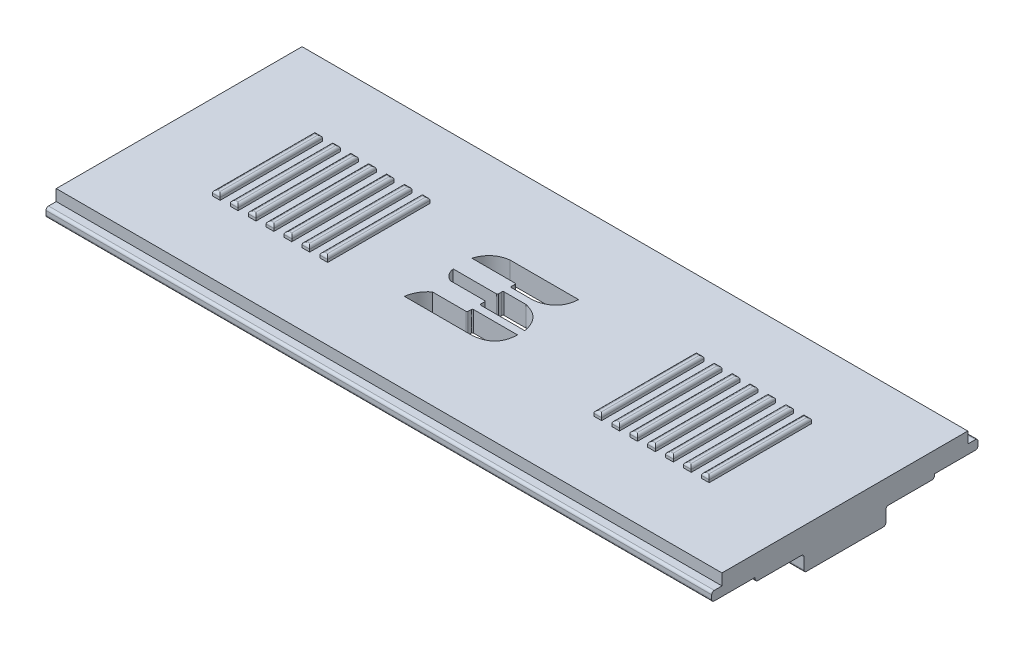
SolidWorks part; units mm, degrees
ref_plane "Front Plane" through (0, 0, 0) normal (0, 0, 1) x (1, 0, 0)
ref_plane "Top Plane" through (0, 0, 0) normal (0, 1, 0) x (1, 0, 0)
ref_plane "Right Plane" through (0, 0, 0) normal (1, 0, 0) x (0, 0, -1)
sketch "Sketch1" plane through (0, 0, 0) normal (0, 1, 0) x (1, 0, 0)
  line L1 (0, 0) -> (-65, 0)
  line L2 (0, 0) -> (0, 28)
  line L3 (0, 28) -> (-65, 28)
  line L4 (-65, 0) -> (-65, 28)
  dimension "D1" = 65
  dimension "D2" = 28
extrude "Boss-Extrude1" add sketch "Sketch1" along normal blind 2
sketch "Sketch2" plane through (0, 2, 0) normal (0, 1, 0) x (1, 0, 0)
  line L0 (-65, 28) -> (-65, 0) construction
  line L2 (-39, 9.4351) -> (-39, 19.8)
  line L3 (-39, 19.8) -> (-45.078, 19.8)
  line L5 (0, 28) -> (-65, 28) construction
  line L6 (-45.078, 19.8) -> (-45.078, 13.1703)
  line L7 (-45.078, 13.1703) -> (-39, 13.1703)
  line L8 (-39, 9.4351) -> (-45.078, 9.4351)
  line L9 (-45.078, 9.4351) -> (-45.078, 16.0649)
  line L10 (-45.078, 16.0649) -> (-39, 16.0649)
  line L11 (-45.078, 16.0649) -> (-45.078, 13.1703)
  point P6 (-42.039, 19.8)
  dimension "D1" = 26
  dimension "D2" = 8.2
sketch "Sketch5" plane through (0, 2, 0) normal (0, 1, 0) x (1, 0, 0)
  line L69 (-34.5, 28) -> (-34.5, 0) construction
  line L70 (-30.1108, 18.1128) -> (-36.82, 18.1128)
  line L86 (-34.5, 14) -> (-65, 14) construction
  line L87 (-65, 28) -> (-65, 0) construction
  line L157 (-38.8269, 16.4025) -> (-34.6166, 16.4025)
  line L158 (-34.5132, 16.3274) -> (-34.5132, 15.9551)
  line L159 (-34.4285, 15.8453) -> (-32.2293, 15.8453)
  line L160 (-34.4186, 15.1333) -> (-32.2791, 15.1333)
  line L161 (-34.5132, 14.6729) -> (-34.5132, 15.0121)
  line L162 (-34.6166, 14.5874) -> (-38.8269, 14.5874)
  line L163 (-37.9572, 13.4446) -> (-34.6166, 13.4446)
  line L164 (-34.5132, 13.3644) -> (-34.5132, 12.9776)
  line L165 (-34.4131, 12.859) -> (-30.1108, 12.859)
  line L166 (-30.1108, 12.1455) -> (-34.4131, 12.1455)
  line L167 (-34.5132, 12.0357) -> (-34.5132, 11.725)
  line L168 (-34.6166, 11.627) -> (-37.9062, 11.627)
  line L169 (-38.8924, 9.8833) -> (-32.2102, 9.8833)
  spline S0 degree 2 poles (-30.1108, 18.1128) (-30.2266, 16.1766) (-32.2293, 15.8453) knots 0 0 0 1 1 1
  spline S1 degree 2 poles (-36.82, 18.1128) (-38.3422, 17.8962) (-38.8269, 16.4025) knots 0 0 0 1 1 1
  spline S2 degree 2 poles (-32.2791, 15.1333) (-30.444, 14.7354) (-30.1108, 12.859) knots 0 0 0 1 1 1
  spline S3 degree 2 poles (-38.8269, 14.5874) (-38.7018, 13.7846) (-37.9572, 13.4446) knots 0 0 0 1 1 1
  spline S4 degree 2 poles (-37.9062, 11.627) (-38.7379, 10.948) (-38.8924, 9.8833) knots 0 0 0 1 1 1
  spline S5 degree 2 poles (-30.1108, 12.1455) (-30.1355, 10.1172) (-32.2102, 9.8833) knots 0 0 0 1 1 1
  spline S6 degree 2 poles (-34.6166, 16.4025) (-34.5203, 16.4078) (-34.5132, 16.3274) knots 0 0 0 1 1 1
  spline S7 degree 2 poles (-34.5132, 15.9551) (-34.5132, 15.8685) (-34.4285, 15.8453) knots 0 0 0 1 1 1
  spline S8 degree 2 poles (-34.4186, 15.1333) (-34.5097, 15.1098) (-34.5132, 15.0121) knots 0 0 0 1 1 1
  spline S9 degree 2 poles (-34.5132, 14.6729) (-34.528, 14.5885) (-34.6166, 14.5874) knots 0 0 0 1 1 1
  spline S10 degree 2 poles (-34.6166, 13.4446) (-34.5199, 13.4532) (-34.5132, 13.3644) knots 0 0 0 1 1 1
  spline S11 degree 2 poles (-34.5132, 12.9776) (-34.5006, 12.8836) (-34.4131, 12.859) knots 0 0 0 1 1 1
  spline S12 degree 2 poles (-34.4131, 12.1455) (-34.5019, 12.1303) (-34.5132, 12.0357) knots 0 0 0 1 1 1
  spline S13 degree 2 poles (-34.6166, 11.627) (-34.5056, 11.6151) (-34.5132, 11.725) knots 0 0 0 1 1 1
  dimension "D1" = 30.5
extrude "Cut-Extrude4" cut sketch "Sketch5" against normal blind 10
fillet "Fillet1" radius 1 4 edges at (0, 1, -28) (0, 1, 0) (-65, 1, 0) (-65, 1, -28)
sketch "Sketch7" plane through (0, 0, 0) normal (1, 0, 0) x (0, 0, -1)
  line L0 (26, 2) -> (26, 0.9)
  line L1 (26, 0.9) -> (27, 0.9)
  line L2 (27, 0.9) -> (27, 0)
  line L3 (27, 0) -> (1, 0)
  line L4 (1, 0) -> (1, 0.9)
  line L5 (1, 0.9) -> (2, 0.9)
  line L6 (2, 0.9) -> (2, 2)
  line L7 (26, 2) -> (2, 2)
  line L8 (1, 0) -> (27, 0) construction
  line L11 (1, 2) -> (1, 0) construction
  dimension "D1" = 0.9
  dimension "D2" = 1.1
  dimension "D3" = 24
  dimension "D4" = 1
extrude "Cut-Extrude6" cut sketch "Sketch7" against normal through all flip side to cut
sketch "Sketch9" plane through (0, 2, 0) normal (0, 1, 0) x (1, 0, 0)
  line L1 (-55, 19) -> (-54.25, 19)
  line L2 (-55, 19) -> (-55, 9)
  line L3 (-55, 9) -> (-54.25, 9)
  line L4 (-54.25, 19) -> (-54.25, 9)
  line L5 (-53.25, 9) -> (-52.5, 9)
  line L6 (-53.25, 9) -> (-53.25, 19)
  line L7 (-53.25, 19) -> (-52.5, 19)
  line L8 (-52.5, 9) -> (-52.5, 19)
  line L9 (-51.5, 9) -> (-50.75, 9)
  line L10 (-51.5, 9) -> (-51.5, 19)
  line L11 (-51.5, 19) -> (-50.75, 19)
  line L12 (-50.75, 9) -> (-50.75, 19)
  line L13 (-49.75, 9) -> (-49, 9)
  line L14 (-49.75, 9) -> (-49.75, 19)
  line L15 (-49.75, 19) -> (-49, 19)
  line L16 (-49, 9) -> (-49, 19)
  line L32 (-65, 26) -> (-65, 2) construction
  line L33 (-65, 26) -> (0, 26) construction
  line L34 (-32.5, 26) -> (-32.5, 20.1111) construction
  line L35 (-48, 19) -> (-47.25, 19)
  line L36 (-48, 19) -> (-48, 9)
  line L37 (-48, 9) -> (-47.25, 9)
  line L38 (-47.25, 19) -> (-47.25, 9)
  line L39 (-19.5, 19) -> (-19.5, 9)
  line L60 (-56, 19) -> (-56.75, 19)
  line L61 (-56, 19) -> (-56, 9)
  line L62 (-56, 9) -> (-56.75, 9)
  line L63 (-56.75, 19) -> (-56.75, 9)
  line L64 (-46.25, 19) -> (-45.5, 19)
  line L65 (-46.25, 19) -> (-46.25, 9)
  line L66 (-46.25, 9) -> (-45.5, 9)
  line L67 (-45.5, 19) -> (-45.5, 9)
  line L68 (-18.75, 9) -> (-19.5, 9)
  line L69 (-18.75, 19) -> (-18.75, 9)
  line L70 (-18.75, 19) -> (-19.5, 19)
  line L71 (-8.25, 19) -> (-8.25, 9)
  line L72 (-9, 9) -> (-8.25, 9)
  line L73 (-9, 19) -> (-9, 9)
  line L74 (-9, 19) -> (-8.25, 19)
  line L75 (-17.75, 19) -> (-17.75, 9)
  line L76 (-17, 9) -> (-17.75, 9)
  line L77 (-17, 19) -> (-17, 9)
  line L78 (-17, 19) -> (-17.75, 19)
  line L79 (-16, 9) -> (-16, 19)
  line L80 (-15.25, 19) -> (-16, 19)
  line L81 (-15.25, 9) -> (-15.25, 19)
  line L82 (-15.25, 9) -> (-16, 9)
  line L83 (-14.25, 9) -> (-14.25, 19)
  line L84 (-13.5, 19) -> (-14.25, 19)
  line L85 (-13.5, 9) -> (-13.5, 19)
  line L86 (-13.5, 9) -> (-14.25, 9)
  line L87 (-12.5, 9) -> (-12.5, 19)
  line L88 (-11.75, 19) -> (-12.5, 19)
  line L89 (-11.75, 9) -> (-11.75, 19)
  line L90 (-11.75, 9) -> (-12.5, 9)
  line L91 (-10.75, 19) -> (-10.75, 9)
  line L92 (-10, 9) -> (-10.75, 9)
  line L93 (-10, 19) -> (-10, 9)
  line L94 (-10, 19) -> (-10.75, 19)
  point P25 (-32.5, 26)
  dimension "D1" = 0.75
  dimension "D2" = 10
  dimension "D3" = 1
  dimension "D4" = 1
  dimension "D5" = 1
  dimension "D6" = 10
  dimension "D7" = 7
  dimension "D8" = 1
  dimension "D9" = 1
  dimension "D10" = 1
sketch "Sketch10" plane through (0, 0, 0) normal (0, -1, 0) x (1, 0, 0)
  line L0 (0, -1) -> (0, -27) construction
  line L1 (0, -18) -> (-4, -18)
  line L2 (0, -18) -> (0, -10)
  line L3 (0, -10) -> (-4, -10)
  line L4 (-4, -18) -> (-4, -10)
  line L5 (-65, -27) -> (0, -27) construction
  line L6 (-65, -1) -> (0, -1) construction
  point P8 (-2, -10)
  dimension "D1" = 9
  dimension "D2" = 9
  dimension "D3" = 4
extrude "Boss-Extrude2" add sketch "Sketch10" along normal blind 2
fillet "Fillet2" radius 0.25 6 edges at (-2, 0, -18) (-2, -2, -18) (-4, 0, -14) (-4, -2, -14) (-2, 0, -10) (-2, -2, -10)
fillet "Fillet3" radius 0.25 4 edges at (-32.5, 0.9, -1) (-32.5, 0, -1) (-32.5, 0.9, -27) (-32.5, 0, -27)
sketch "Sketch11" plane through (0, 0, 0) normal (0, -1, 0) x (1, 0, 0)
  line L0 (0, -18.25) -> (0, -26.75) construction
  line L1 (0, -22.75) -> (-3.5, -22.75)
  line L2 (0, -22.75) -> (0, -5.25)
  line L3 (0, -5.25) -> (-3.5, -5.25)
  line L4 (-3.5, -22.75) -> (-3.5, -5.25)
  line L5 (0, -17.75) -> (0, -10.25) construction
  line L6 (0, -10.25) -> (-3.75, -10.25) construction
  point P8 (0, -14)
  point P9 (0, -14)
  dimension "D1" = 3.5
  dimension "D2" = 0
  dimension "D3" = 5
extrude "Boss-Extrude3" add sketch "Sketch11" along normal blind 0.4
fillet "Fillet4" radius 0.25 2 edges at (-1.75, -0.4, -5.25) (-1.75, -0.4, -22.75)
fillet "Fillet5" radius 0.25 2 edges at (-1.75, -0.4, -18) (-1.75, -0.4, -10)
extrude "Boss-Extrude4" add sketch "Sketch9" along normal blind 0.5
fillet "Fillet9" radius 0.25 56 edges at (-18.75, 2.5, -14) (-19.125, 2.5, -9) (-19.5, 2.5, -14) (-19.125, 2.5, -19) (-17, 2.5, -14) (-17.375, 2.5, -9) (-17.75, 2.5, -14) (-17.375, 2.5, -19) (-16, 2.5, -14) (-15.625, 2.5, -19) (-15.25, 2.5, -14) (-15.625, 2.5, -9) (-14.25, 2.5, -14) (-13.875, 2.5, -19) (-13.5, 2.5, -14) (-13.875, 2.5, -9) (-12.5, 2.5, -14) (-12.125, 2.5, -19) (-11.75, 2.5, -14) (-12.125, 2.5, -9) (-10, 2.5, -14) (-10.375, 2.5, -9) (-10.75, 2.5, -14) (-10.375, 2.5, -19) (-8.25, 2.5, -14) (-8.625, 2.5, -9) (-9, 2.5, -14) (-8.625, 2.5, -19) (-45.875, 2.5, -19) (-45.5, 2.5, -14) (-45.875, 2.5, -9) (-46.25, 2.5, -14) (-47.625, 2.5, -19) (-47.25, 2.5, -14) (-47.625, 2.5, -9) (-48, 2.5, -14) (-49.375, 2.5, -19) (-49, 2.5, -14) (-49.375, 2.5, -9) (-49.75, 2.5, -14) (-51.125, 2.5, -19) (-50.75, 2.5, -14) (-51.125, 2.5, -9) (-51.5, 2.5, -14) (-52.875, 2.5, -19) (-52.5, 2.5, -14) (-52.875, 2.5, -9) (-53.25, 2.5, -14) (-54.625, 2.5, -19) (-54.25, 2.5, -14) (-54.625, 2.5, -9) (-55, 2.5, -14) (-56.375, 2.5, -9) (-56.75, 2.5, -14) (-56.375, 2.5, -19) (-56, 2.5, -14)
